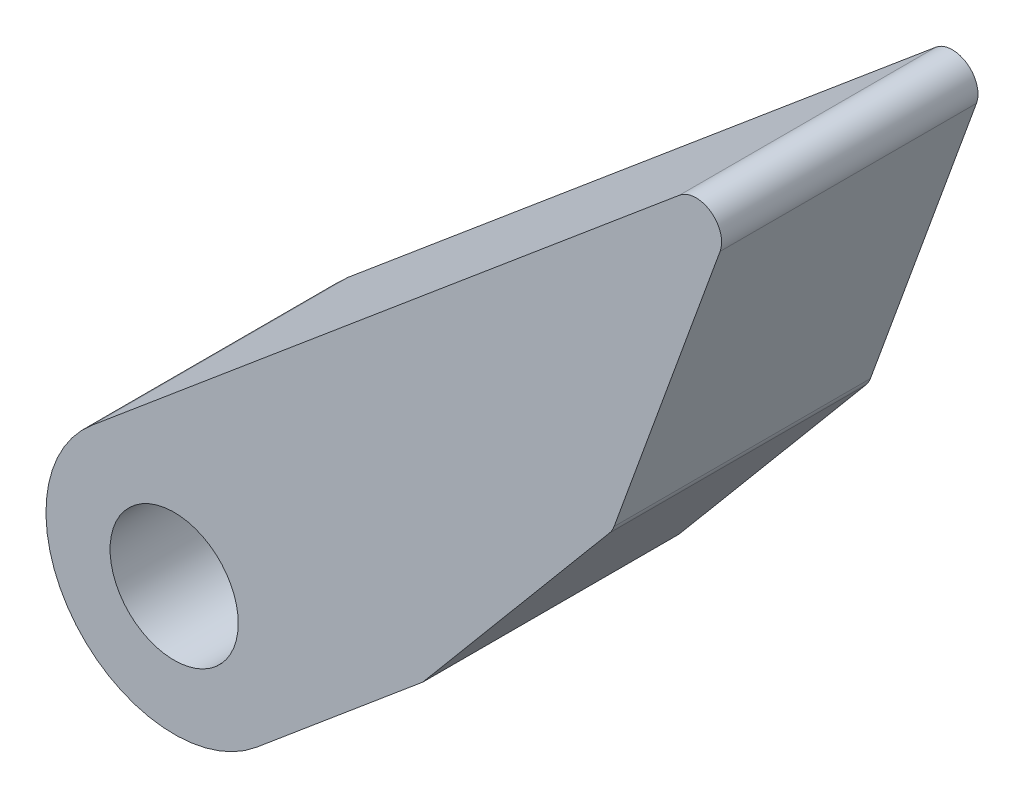
SolidWorks part; units mm, degrees
ref_plane "前基準面" through (0, 0, 0) normal (0, 0, 1) x (1, 0, 0)
ref_plane "上基準面" through (0, 0, 0) normal (0, 1, 0) x (1, 0, 0)
ref_plane "右基準面" through (0, 0, 0) normal (1, 0, 0) x (0, 0, -1)
sketch "草圖1" plane through (0, 0, 0) normal (0, 0, 1) x (1, 0, 0)
  line L0 (-35.89, -24.2957) -> (57.2739, 53.8781) construction
  line L1 (-35.89, -24.2957) -> (43.1518, -24.2957) construction
  line L2 (-23.5205, -7.3894) -> (-17.7752, -2.5685) construction
  line L3 (-13.7163, 4.9284) -> (-17.8519, -6.434)
  line L4 (-25.3155, -15.4227) -> (-31.7972, -20.8615)
  line L6 (-38.2251, -13.201) -> (-15.2988, 6.0364)
  line L7 (-18.0255, -6.7348) -> (-25.3155, -15.4227)
  line L11 (-35.0112, -17.0313) -> (-35.5793, -20.4417) construction
  circle A0 centre (-23.5205, -7.3894) radius 2.5 construction
  circle A1 centre (-17.7752, -2.5685) radius 5 construction
  circle A2 centre (-12.0298, 2.2524) radius 2.5 construction
  arc A3 (-38.8414, -20.2452) -> (-31.7972, -20.8615) centre (-35.0112, -17.0313) ccw
  circle A4 centre (-35.0112, -17.0313) radius 2.5
  arc A5 (-18.0255, -6.7348) -> (-17.8519, -6.434) centre (-18.7916, -6.092) ccw
  arc A6 (-13.7163, 4.9284) -> (-15.2988, 6.0364) centre (-14.656, 5.2704) ccw
  arc A7 (-38.8414, -20.2452) -> (-38.2251, -13.201) centre (-35.0112, -17.0313) cw
  point P12 (0, 0)
  point P16 (-33.2821, -22.1074)
  point P20 (-33.2821, -22.1074)
  point P21 (-22.6865, -13.2167)
  point P22 (-16.1422, -3.3773)
  point P23 (-26.7534, -16.6292)
  point P25 (-15.6348, -3.5726)
  point P28 (-17.9122, -6.5997)
  point P33 (0, 0)
  dimension "D2" = 5
  dimension "D3" = 10
  dimension "D5" = 10
  dimension "D6" = 5
  dimension "D8" = 5
  dimension "D12" = 1
  dimension "D13" = 5
  dimension "D1" = 40
  dimension "D4" = 5
  dimension "D7" = 15
  dimension "D9" = 10
  dimension "D10" = 30
  dimension "D11" = 8
extrude "填料-伸長1" add sketch "草圖1" along normal blind 10
